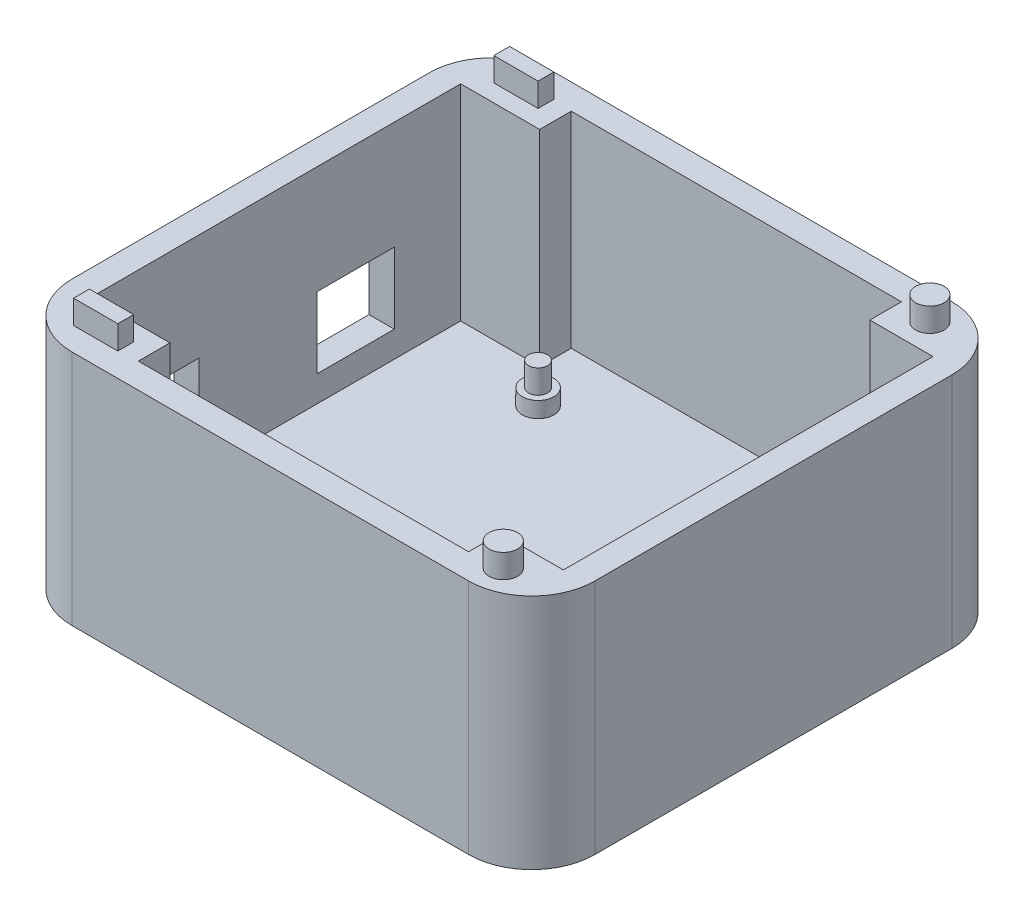
SolidWorks part; units mm, degrees
ref_plane "Front Plane" through (0, 0, 0) normal (0, 0, 1) x (1, 0, 0)
ref_plane "Top Plane" through (0, 0, 0) normal (0, 1, 0) x (1, 0, 0)
ref_plane "Right Plane" through (0, 0, 0) normal (1, 0, 0) x (0, 0, -1)
sketch "Sketch1" plane through (0, 0, 0) normal (0, 1, 0) x (1, 0, 0)
  line L1 (-42.037, -38.862) -> (42.037, -38.862)
  line L2 (-42.037, -38.862) -> (-42.037, 38.862)
  line L3 (-42.037, 38.862) -> (42.037, 38.862)
  line L4 (42.037, -38.862) -> (42.037, 38.862)
  line L5 (-42.037, -38.862) -> (42.037, 38.862) construction
  line L6 (-42.037, 38.862) -> (42.037, -38.862) construction
  point P0 (0, 0)
extrude "Boss-Extrude1" add sketch "Sketch1" along normal blind 5.08
sketch "Sketch2" plane through (0, 5.08, 0) normal (0, 1, 0) x (1, 0, 0)
  line L1 (-42.037, 38.862) -> (-42.037, -38.862) construction
  line L2 (42.037, 38.862) -> (-42.037, 38.862) construction
  point P0 (-19.939, 24.13)
  point P1 (-19.939, -24.13)
  point P2 (30.861, 8.89)
  point P3 (30.861, -19.05)
  dimension "D2" = 22.098
  dimension "D3" = 14.732
  dimension "D4" = 50.8
  dimension "D5" = 50.8
  dimension "D6" = 15.24
  dimension "D7" = 27.94
  dimension "D8" = 5.08
  dimension "D9" = 48.26
  dimension "D10" = 0
sketch "Sketch3" plane through (0, 5.08, 0) normal (0, 1, 0) x (1, 0, 0)
  circle A0 centre (-19.939, 24.13) radius 2.54
  circle A1 centre (-19.939, -24.13) radius 2.54
  circle A2 centre (30.861, 8.89) radius 2.54
  circle A3 centre (30.861, -19.05) radius 2.54
extrude "Boss-Extrude2" add sketch "Sketch3" along normal blind 2.54
sketch "Sketch19" plane through (0, 5.08, 0) normal (0, 1, 0) x (1, 0, 0)
  line L0 (42.037, -38.862) -> (42.037, 38.862) construction
  line L1 (-42.037, 38.862) -> (42.037, 38.862)
  line L2 (-42.037, 38.862) -> (-42.037, 34.798)
  line L3 (-42.037, 34.798) -> (42.037, 34.798)
  line L4 (42.037, 38.862) -> (42.037, 34.798)
  line L5 (-42.037, -38.862) -> (42.037, -38.862) construction
  line L6 (42.037, 34.798) -> (37.973, 34.798)
  line L7 (42.037, 34.798) -> (42.037, -38.862)
  line L8 (42.037, -38.862) -> (37.973, -38.862)
  line L9 (37.973, 34.798) -> (37.973, -38.862)
  line L10 (-42.037, 38.862) -> (-42.037, -38.862) construction
  line L11 (37.973, -38.862) -> (-42.037, -38.862)
  line L12 (37.973, -38.862) -> (37.973, -34.798)
  line L13 (37.973, -34.798) -> (-42.037, -34.798)
  line L14 (-42.037, -38.862) -> (-42.037, -34.798)
  line L16 (-42.037, 34.798) -> (-37.973, 34.798)
  line L17 (-42.037, 34.798) -> (-42.037, -34.798)
  line L18 (-42.037, -34.798) -> (-37.973, -34.798)
  line L19 (-37.973, 34.798) -> (-37.973, -34.798)
  line L20 (-37.973, 34.798) -> (-25.273, 34.798)
  line L21 (-37.973, 34.798) -> (-37.973, 29.718)
  line L22 (-37.973, 29.718) -> (-25.273, 29.718)
  line L23 (-25.273, 34.798) -> (-25.273, 29.718)
  line L24 (37.973, 34.798) -> (27.813, 34.798)
  line L25 (37.973, 34.798) -> (37.973, 29.718)
  line L26 (37.973, 29.718) -> (27.813, 29.718)
  line L27 (27.813, 34.798) -> (27.813, 29.718)
  line L28 (37.973, -34.798) -> (27.813, -34.798)
  line L29 (37.973, -34.798) -> (37.973, -29.718)
  line L30 (37.973, -29.718) -> (27.813, -29.718)
  line L31 (27.813, -34.798) -> (27.813, -29.718)
  line L32 (-37.973, -34.798) -> (-25.273, -34.798)
  line L33 (-37.973, -34.798) -> (-37.973, -29.718)
  line L34 (-37.973, -29.718) -> (-25.273, -29.718)
  line L35 (-25.273, -34.798) -> (-25.273, -29.718)
  line M26 (42.037, -38.862) -> (42.037, 38.862)
  line M27 (42.037, 38.862) -> (-42.037, 38.862)
  line M28 (-42.037, 38.862) -> (-42.037, -38.862)
  line M29 (-42.037, -38.862) -> (42.037, -38.862)
  dimension "D1" = 4.064
  dimension "D2" = 4.064
  dimension "D3" = 4.064
  dimension "D4" = 4.064
  dimension "D5" = 12.7
  dimension "D6" = 5.08
  dimension "D7" = 10.16
  dimension "D8" = 5.08
  dimension ".5" = 10.16
  dimension "D10" = 5.08
  dimension "D11" = 12.7
  dimension "D12" = 5.08
extrude "Boss-Extrude7" add sketch "Sketch19" along normal blind 33.02 contours L19 L3 L13 M28 | L13 L35 L34 L19 | L3 L9 M29 M26 | L3 L27 L26 L9 | L3 M28 M26 M27 | L23 L3 L19 L22 | L9 L13 M28 M29 | L29 L30 L31 L28
fillet "Fillet2" radius 10.16 4 edges at (-42.037, 19.05, -38.862) (-42.037, 19.05, 38.862) (42.037, 19.05, -38.862) (42.037, 19.05, 38.862)
sketch "Sketch21" plane through (0, 38.1, 0) normal (0, 1, 0) x (1, 0, 0)
  line L0 (-42.037, 28.702) -> (-42.037, -28.702) construction
  line L1 (31.877, 38.862) -> (-31.877, 38.862) construction
  line L2 (42.037, -28.702) -> (42.037, 28.702) construction
  line L3 (-35.433, 32.512) -> (-28.321, 32.512)
  line L4 (-35.433, 32.512) -> (-35.433, 35.052)
  line L5 (-35.433, 35.052) -> (-28.321, 35.052)
  line L6 (-28.321, 32.512) -> (-28.321, 35.052)
  line L7 (-35.433, 32.512) -> (-28.321, 35.052) construction
  line L8 (-35.433, 35.052) -> (-28.321, 32.512) construction
  circle A0 centre (32.893, 34.29) radius 2.286
  point P0 (-31.877, 33.782)
  point P5 (-31.877, 33.782)
  dimension "D3" = 9.144
  dimension "D1" = 10.16
  dimension "D2" = 5.08
  dimension "D4" = 4.572
extrude "Boss-Extrude9" add sketch "Sketch21" along normal blind 3.81
sketch "Sketch22" plane through (-42.037, 0, 0) normal (-1, 0, 0) x (0, 0, 1)
  line L1 (-28.702, 0) -> (28.702, 0) construction
  line L2 (-38.862, 0) -> (-38.862, 38.1) construction
  line L4 (-19.05, 20.701) -> (-6.604, 20.701)
  line L5 (-19.05, 20.701) -> (-19.05, 9.271)
  line L6 (-19.05, 9.271) -> (-6.604, 9.271)
  line L7 (-6.604, 20.701) -> (-6.604, 9.271)
  line L8 (12.319, 20.9543) -> (22.098, 20.9543)
  line L9 (12.319, 20.9543) -> (12.319, 9.271)
  line L10 (12.319, 9.271) -> (22.098, 9.271)
  line L11 (22.098, 20.9543) -> (22.098, 9.271)
  point P0 (-19.05, 9.271)
  point P3 (-6.604, 9.271)
  point P4 (-19.05, 20.701)
  point P5 (-6.604, 20.7009)
  point P8 (12.446, 9.271)
  point P9 (22.098, 9.271)
  point P10 (12.319, 20.9543)
  point P11 (22.098, 20.955)
  dimension "D1" = 9.271
  dimension "D2" = 12.446
  dimension "D3" = 11.43
  dimension "D4" = 19.812
  dimension "D5" = 12.446
  dimension "D6" = 19.05
  dimension "D7" = 9.652
  dimension "D8" = 11.684
  dimension "D9" = 11.684
  dimension "D10" = 9.652
extrude "Cut-Extrude10" cut sketch "Sketch22" against normal blind 5.08
sketch "Sketch23" plane through (0, 7.62, 0) normal (0, 1, 0) x (1, 0, 0)
  circle A0 centre (-19.939, 24.13) radius 1.524
  circle A1 centre (30.861, 8.89) radius 1.524
  circle A2 centre (-19.939, -24.13) radius 1.524
  circle A3 centre (30.861, -19.05) radius 1.524
extrude "Boss-Extrude10" add sketch "Sketch23" along normal blind 3.81
mirror "Mirror1" about plane through (0, 0, 0) normal (0, 0, 1) of "Boss-Extrude9"
